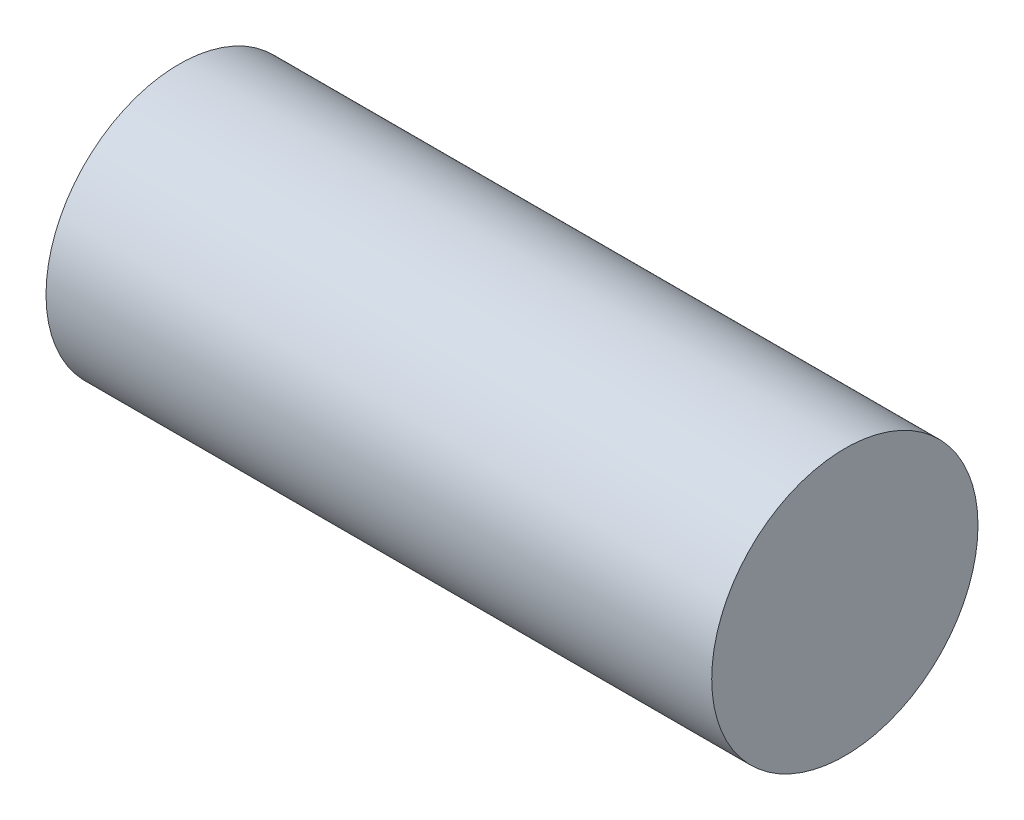
SolidWorks part; units mm, degrees
ref_plane "Front Plane" through (0, 0, 0) normal (0, 0, 1) x (1, 0, 0)
ref_plane "Top Plane" through (0, 0, 0) normal (0, 1, 0) x (1, 0, 0)
ref_plane "Right Plane" through (0, 0, 0) normal (1, 0, 0) x (0, 0, -1)
sketch "Sketch1" plane through (0, 0, 0) normal (1, 0, 0) x (0, 0, -1)
  circle A0 centre (0, 0) radius 0.2
  dimension "D1" = 0.4
extrude "Boss-Extrude1" add sketch "Sketch1" along normal blind 1
